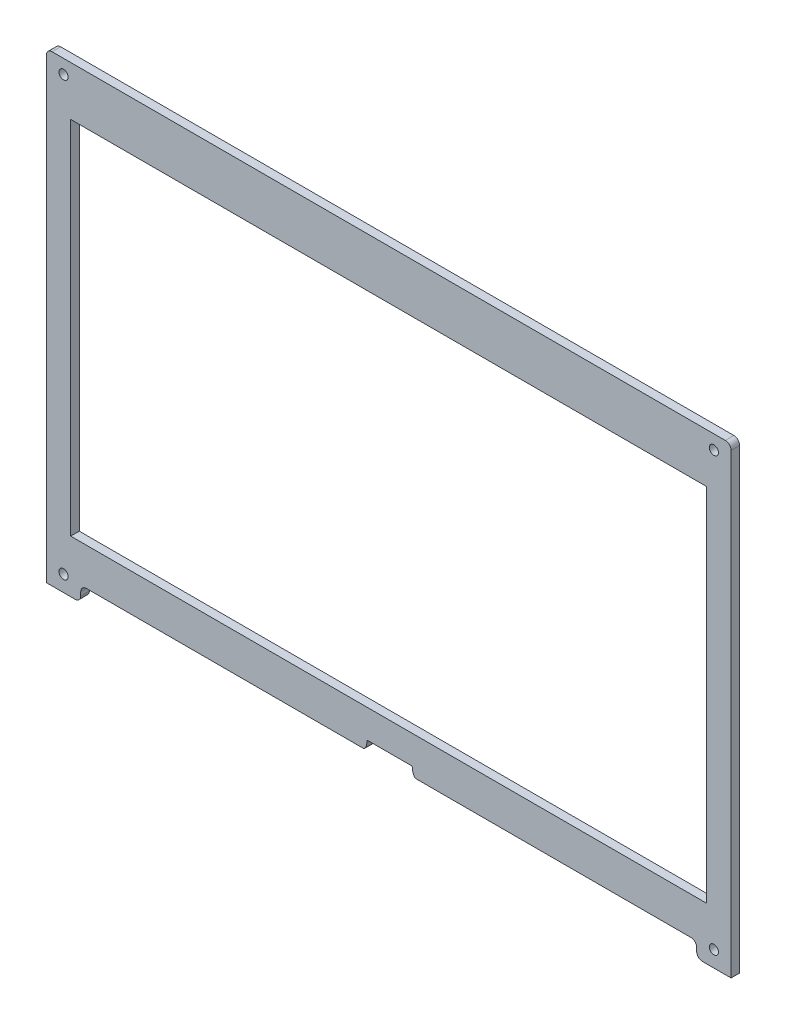
SolidWorks part; units mm, degrees
ref_plane "Front Plane" through (0, 0, 0) normal (0, 0, 1) x (1, 0, 0)
ref_plane "Top Plane" through (0, 0, 0) normal (0, 1, 0) x (1, 0, 0)
ref_plane "Right Plane" through (0, 0, 0) normal (1, 0, 0) x (0, 0, -1)
sketch "Sketch1" plane through (0, 0, 0) normal (0, 0, 1) x (1, 0, 0)
  line L26 (-8.8261, -74.3426) -> (-105.5, -74.3426)
  line L28 (-119.5, 79.9139) -> (-119.5, 0)
  line L52 (-117.5, 81.9139) -> (117.4948, 81.9155)
  line L54 (-119.5, 0) -> (-119.5, -78.8888)
  line L55 (-119.5, -78.8888) -> (-119.4901, -78.8888)
  line L56 (-119.5, -78.8888) -> (-119.5, -79.5888)
  line L57 (-119.5, -79.5888) -> (-109.5, -79.5888)
  line L58 (119.5, 79.87) -> (119.5, -78.8888) construction
  line L60 (107.5, -78.8888) -> (107.5, -72.0459) construction
  line L61 (107.5, -72.0459) -> (-107.5, -72.0459) construction
  line L62 (107.5, -78.8888) -> (-107.5, -78.8888) construction
  line L63 (-107.5, -72.0459) -> (-107.5, -78.8888) construction
  line L66 (107.5, -72.0459) -> (107.5, -77.5888)
  line L67 (-119.5, 0) -> (120.1784, 0) construction
  line L69 (-107.5, -76.3426) -> (-107.5, -77.5888)
  line L70 (-110.9987, 64.7083) -> (111.017, 64.7083)
  line L71 (-110.9987, 64.7083) -> (-110.9987, -61.2641)
  line L73 (111.017, 64.7083) -> (111.017, -61.2641)
  line L77 (119.5, 79.9103) -> (119.5, -78.8888)
  line L79 (119.5, -78.8888) -> (119.5, -79.5888)
  line L80 (0, 81.9139) -> (0, 0) construction
  line L81 (0, 0) -> (0, -78.8888) construction
  line L82 (9.4659, -74.3426) -> (105.5, -74.3426)
  line L83 (-7.1608, -71.1942) -> (7.8392, -71.1942)
  line L84 (-7.6614, -72.2343) -> (-7.6608, -71.6937)
  line L85 (8.3392, -71.6937) -> (8.3387, -72.1543)
  line L86 (0, 81.9139) -> (0, -78.8888) construction
  line L87 (-110.9987, -61.2641) -> (111.017, -61.2641)
  line L88 (-119.5, -78.8888) -> (-119.4901, -78.8888)
  line L89 (119.5, -79.5888) -> (109.5, -79.5888)
  arc A30 (117.4948, 81.9155) -> (119.5, 79.9103) centre (117.4948, 79.9103) cw
  arc A31 (-109.5, -79.5888) -> (-107.5, -77.5888) centre (-109.5, -77.5888) ccw
  arc A32 (107.5, -77.5888) -> (109.5, -79.5888) centre (109.5, -77.5888) ccw
  circle A37 centre (-113.5, 77.0143) radius 1.6031 construction
  circle A38 centre (113.5, 77.0112) radius 1.6 construction
  circle A39 centre (113.5, -73.9888) radius 1.6074 construction
  circle A40 centre (-113.5, -73.9888) radius 1.6 construction
  arc A41 (-117.5, 81.9122) -> (-119.5, 79.9139) centre (-117.5, 79.9122) ccw construction
  arc A42 (117.4948, 81.9155) -> (119.5, 79.87) centre (117.4948, 79.9099) cw construction
  circle A43 centre (-113.5, 77.0143) radius 1.6
  circle A44 centre (113.5, 77.0112) radius 1.6
  circle A45 centre (113.5, -73.9888) radius 1.5909
  circle A46 centre (-113.5, -73.9888) radius 1.6105
  arc A49 (-105.5, -74.3426) -> (-107.5, -76.3426) centre (-105.5, -76.3426) ccw
  arc A51 (105.5, -74.3426) -> (107.5, -76.3426) centre (105.5, -76.3426) cw
  arc A52 (-119.5, 79.9139) -> (-117.5, 81.9139) centre (-117.5, 79.9139) cw
  arc A53 (-7.6614, -72.2343) -> (-8.4606, -74.1838) centre (-10.6337, -72.1543) cw
  arc A54 (-7.6608, -71.6937) -> (-7.1608, -71.1942) centre (-7.1608, -71.6942) cw
  arc A55 (8.3387, -72.1543) -> (9.1408, -74.1858) centre (11.3121, -72.1543) ccw
  arc A56 (8.3392, -71.6937) -> (7.8392, -71.1942) centre (7.8392, -71.6942) ccw
  arc A57 (9.4659, -74.3426) -> (9.1408, -74.1858) centre (9.5059, -73.8442) cw
  arc A58 (-8.4606, -74.1838) -> (-8.8261, -74.3426) centre (-8.826, -73.8426) cw
  point P97 (-107.5, -74.3426)
  point P98 (0.3392, -74.3426)
  point P113 (-110.9987, 64.7083)
  point P120 (-117.5972, 79.9139)
  point P121 (120.1784, -77.9139)
  point P126 (-113.597, 76.9859)
  point P131 (0.3392, -71.1942)
  dimension "D2" = 2
  dimension "D3" = 2
  dimension "D4" = 2
  dimension "D5" = 2
  dimension "D9" = 0.5
  dimension "D10" = 0.5
extrude "Boss-Extrude1" add sketch "Sketch1" along normal blind 3
